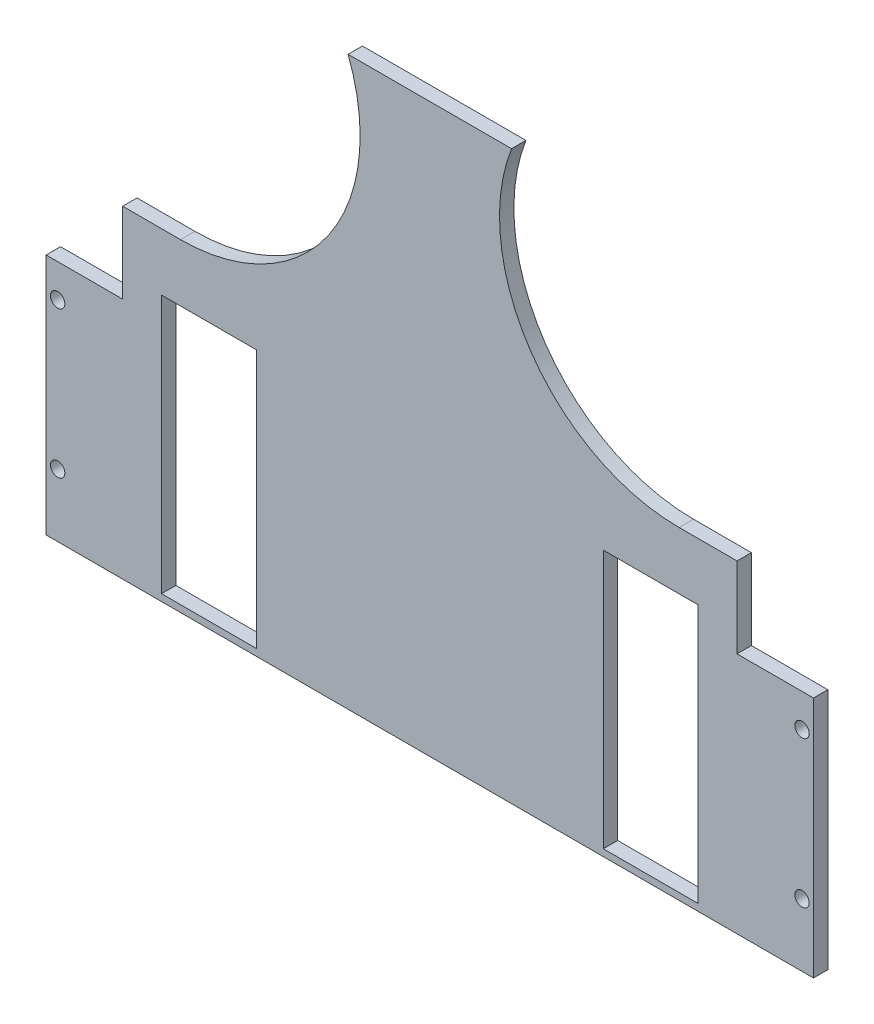
SolidWorks part; units mm, degrees
ref_plane "Front Plane" through (0, 0, 0) normal (0, 0, 1) x (1, 0, 0)
ref_plane "Top Plane" through (0, 0, 0) normal (0, 1, 0) x (1, 0, 0)
ref_plane "Right Plane" through (0, 0, 0) normal (1, 0, 0) x (0, 0, -1)
sketch "Sketch1" plane through (0, 0, 0) normal (0, 0, 1) x (1, 0, 0)
  line L0 (-1087.1, -69) -> (-1087.1, -336.4) construction
  line L1 (-1220.6, -69) -> (-953.6, -69)
  line L2 (-1220.6, -69) -> (-1220.6, -336.4)
  line L3 (-1220.6, -336.4) -> (-953.6, -336.4)
  line L4 (-953.6, -69) -> (-953.6, -336.4)
  line L9 (-1026.74, -174) -> (-993.74, -174)
  line L10 (-1026.74, -174) -> (-1026.74, -264)
  line L11 (-1026.74, -264) -> (-993.74, -264)
  line L12 (-993.74, -174) -> (-993.74, -264)
  line L13 (-1062.8504, -69) -> (-1111.3496, -69) construction
  line L14 (-1180.46, -219) -> (-993.74, -219) construction
  line L15 (-953.6, -336.4) -> (-953.6, -182) construction
  line L21 (-1220.6, -182) -> (-1220.6, -336.4) construction
  line L25 (-953.6, -336.4) -> (-1024.6, -336.4) construction
  line L52 (-1007.74, -174) -> (-1007.74, -264) construction
  line L53 (-1017.74, -174) -> (-997.74, -174) construction
  line L54 (-1017.74, -174) -> (-1017.74, -264) construction
  line L55 (-1017.74, -264) -> (-997.74, -264) construction
  line L56 (-997.74, -174) -> (-997.74, -264) construction
  line L102 (-957.6, -193.5) -> (-957.6, -244.5) construction
  line L103 (-993.74, -219) -> (-957.6, -219) construction
  line L134 (-1180.46, -219) -> (-1216.6, -219) construction
  line L135 (-1216.6, -193.5) -> (-1216.6, -244.5) construction
  line L139 (-1176.46, -174) -> (-1176.46, -264) construction
  line L140 (-1156.46, -264) -> (-1176.46, -264) construction
  line L141 (-1156.46, -174) -> (-1156.46, -264) construction
  line L142 (-1156.46, -174) -> (-1176.46, -174) construction
  line L143 (-1166.46, -174) -> (-1166.46, -264) construction
  line L154 (-1180.46, -174) -> (-1180.46, -264)
  line L155 (-1147.46, -264) -> (-1180.46, -264)
  line L156 (-1147.46, -174) -> (-1147.46, -264)
  line L157 (-1147.46, -174) -> (-1180.46, -174)
  circle A84 centre (-957.6, -193.5) radius 2.5
  circle A85 centre (-957.6, -244.5) radius 2.5
  circle A236 centre (-1216.6, -244.5) radius 2.5
  circle A237 centre (-1216.6, -193.5) radius 2.5
  dimension "D5" = 20
  dimension "D15" = 5
  dimension "D16" = 5
  dimension "D2" = 105
  dimension "D3" = 4
  dimension "D4" = 90
  dimension "D6" = 90
  dimension "D7" = 9
  dimension "D14" = 89.36
  dimension "D17" = 25.5
  dimension "D18" = 4
extrude "Boss-Extrude1" add sketch "Sketch1" along normal blind 5
ref_plane "Plane1"
sketch "Sketch6" plane through (0, 0, 5) normal (0, 0, 1) x (1, 0, 0)
  line L13 (-953.6, -336.4) -> (-953.6, -69) construction
  line L17 (-1058.6599, -69) -> (-953.6, -69)
  line L19 (-1193.9957, -154) -> (-1173.8496, -154) construction
  line L24 (-1220.6, -336.4) -> (-953.6, -336.4)
  line L26 (-1220.6, -336.4) -> (-1220.6, -266.3756)
  line L27 (-953.6, -336.4) -> (-953.6, -266.3756)
  line L28 (-1220.6, -266.3756) -> (-953.6, -266.3756)
  line L30 (-953.6, -69) -> (-1220.6, -69) construction
  line L32 (-953.6, -69) -> (-953.6, -182)
  line L33 (-953.6, -336.4) -> (-953.6, -69) construction
  line L34 (-953.6, -182) -> (-980.2043, -182)
  line L35 (-980.2043, -182) -> (-980.2043, -154)
  line L36 (-980.2043, -154) -> (-1000.3504, -154)
  line L37 (-1000.3504, -154) -> (-970.95, -154) construction
  line L38 (-1115.5401, -69) -> (-1220.6, -69)
  line L39 (-1220.6, -69) -> (-1220.6, -182)
  line L40 (-1220.6, -69) -> (-1220.6, -336.4) construction
  line L41 (-1220.6, -182) -> (-1193.9957, -182)
  line L42 (-1193.9957, -182) -> (-1193.9957, -154)
  line L44 (-1193.9957, -182) -> (-1193.9957, -154) construction
  line L45 (-1193.9957, -154) -> (-1173.8496, -154)
  arc A4 (-1173.8496, -154) -> (-1111.3496, -91.5) centre (-1173.8496, -91.5) ccw construction
  arc A5 (-1058.6599, -69) -> (-1000.3504, -154) centre (-1000.3504, -91.5) ccw construction
  arc A6 (-1000.3504, -154) -> (-1058.6599, -69) centre (-1000.3504, -91.5) cw
  arc A7 (-1173.8496, -154) -> (-1115.5401, -69) centre (-1173.8496, -91.5) ccw
  dimension "D1" = 62.5
extrude "Cut-Extrude4" cut sketch "Sketch6" against normal through all
